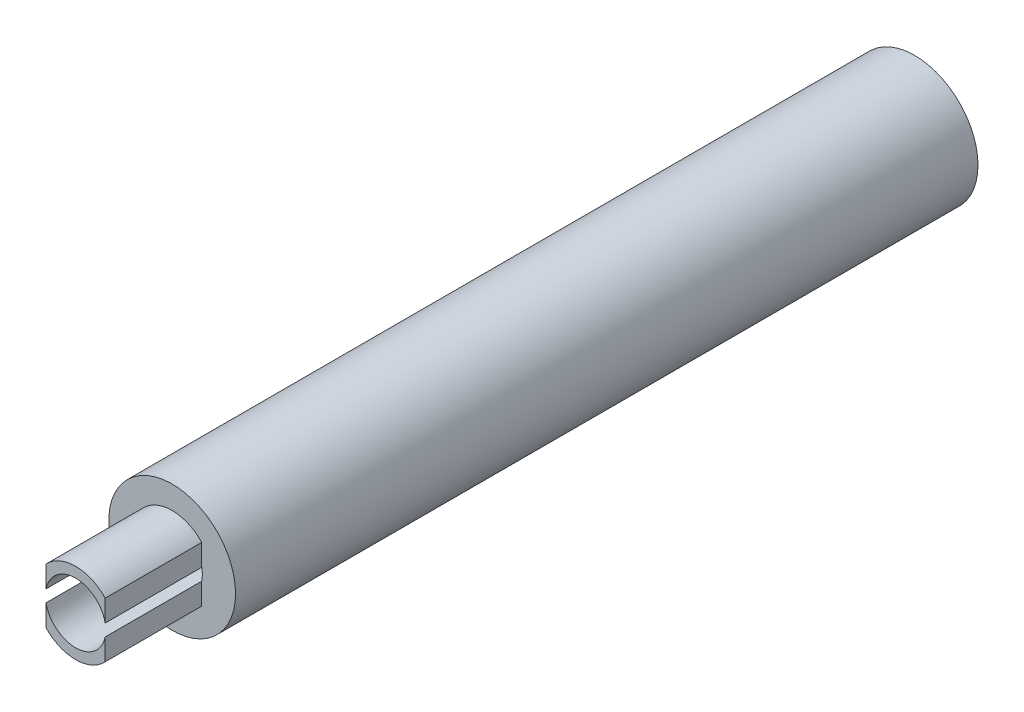
SolidWorks part; units mm, degrees
material "Mosiądz"
ref_plane "Płaszczyzna przednia" through (0, 0, 0) normal (0, 0, 1) x (1, 0, 0)
ref_plane "Płaszczyzna górna" through (0, 0, 0) normal (0, 1, 0) x (1, 0, 0)
ref_plane "Płaszczyzna prawa" through (0, 0, 0) normal (1, 0, 0) x (0, 0, -1)
sketch "Szkic1" plane through (0, 0, 0) normal (0, 0, 1) x (1, 0, 0)
  circle A0 centre (0, 0) radius 5.25
  dimension "D1" = 10.5
extrude "Dodanie-wyciągnięcie1" add sketch "Szkic1" along normal blind 61.5
sketch "Szkic3" plane through (0, 0, 61.5) normal (0, 0, 1) x (1, 0, 0)
  circle A0 centre (0, 0) radius 3.35
extrude "Dodanie-wyciągnięcie2" add sketch "Szkic3" along normal up to surface (8 mm away)
sketch "Szkic4" plane through (0, 0, 69.5) normal (0, 0, 1) x (1, 0, 0)
  circle A0 centre (0, 0) radius 2.5
extrude "Wytnij-wyciągnięcie2" cut sketch "Szkic4" against normal through all
sketch "Szkic7" plane through (0, 0, 0) normal (0, 0, -1) x (-1, 0, 0)
  circle A0 centre (0, 0) radius 3.05
  dimension "D1" = 6.1
extrude "Wytnij-wyciągnięcie4" cut sketch "Szkic7" against normal blind 18
sketch "Szkic8" plane through (0, 0, 61.5) normal (0, 0, 1) x (1, 0, 0)
  line L1 (0, -1.5) -> (-3.952, -1.5)
  line L2 (-3.952, -1.5) -> (-3.952, 1.5)
  line L3 (-3.952, 1.5) -> (3.8949, 1.5)
  line L4 (3.8949, 1.5) -> (3.8949, -1.5)
  line L5 (3.8949, -1.5) -> (0, -1.5)
extrude "Wytnij-wyciągnięcie5" [suppressed] cut sketch "Szkic8" along normal up to surface (8 mm away)
sketch "Szkic9" plane through (0, 0, 61.5) normal (0, 0, 1) x (1, 0, 0)
  line L2 (-4, -6.4676) -> (-7.8872, -6.4676)
  line L3 (-7.8872, -6.4676) -> (-7.8872, 7.4967)
  line L4 (-4, 7.4967) -> (-7.8872, 7.4967)
  line L5 (-4, -6.4676) -> (-4, 7.4967)
  line L9 (4, 7.4967) -> (4, -6.4676)
  line L10 (4, 7.4967) -> (6.6168, 7.4967)
  line L11 (6.6168, 7.4967) -> (6.6168, -6.4676)
  line L12 (4, -6.4676) -> (6.6168, -6.4676)
extrude "Wytnij-wyciągnięcie6" [suppressed] cut sketch "Szkic9" against normal through all
sketch "Szkic10" plane through (0, 0, 69.5) normal (0, 0, 1) x (1, 0, 0)
  line L0 (-2.5, 4.6165) -> (-2.45, 4.6165)
  line L1 (-2.45, 4.6165) -> (-2.45, -4.1559)
  line L2 (-2.5, 4.6165) -> (-5.8211, 4.6165)
  line L3 (-5.8211, 4.6165) -> (-5.8211, -4.1559)
  line L4 (-5.8211, -4.1559) -> (-2.5, -4.1559)
  line L5 (2.5, 4.6165) -> (2.45, 4.6165)
  line L7 (2.5, 4.6165) -> (5.8929, 4.6165)
  line L8 (5.8929, 4.6165) -> (5.8929, -4.1559)
  line L9 (5.8929, -4.1559) -> (2.5, -4.0554)
  line L11 (-2.45, -4.1559) -> (-2.5, -4.1559)
  line L12 (2.45, 4.6165) -> (2.45, -4.0554)
  line L13 (2.45, -4.0554) -> (2.5, -4.0554)
  circle A1 centre (0, 0) radius 5.25 construction
extrude "Wytnij-wyciągnięcie8" cut sketch "Szkic10" against normal up to surface (8 mm away) up to face at (3.35, 0, 61.5)
